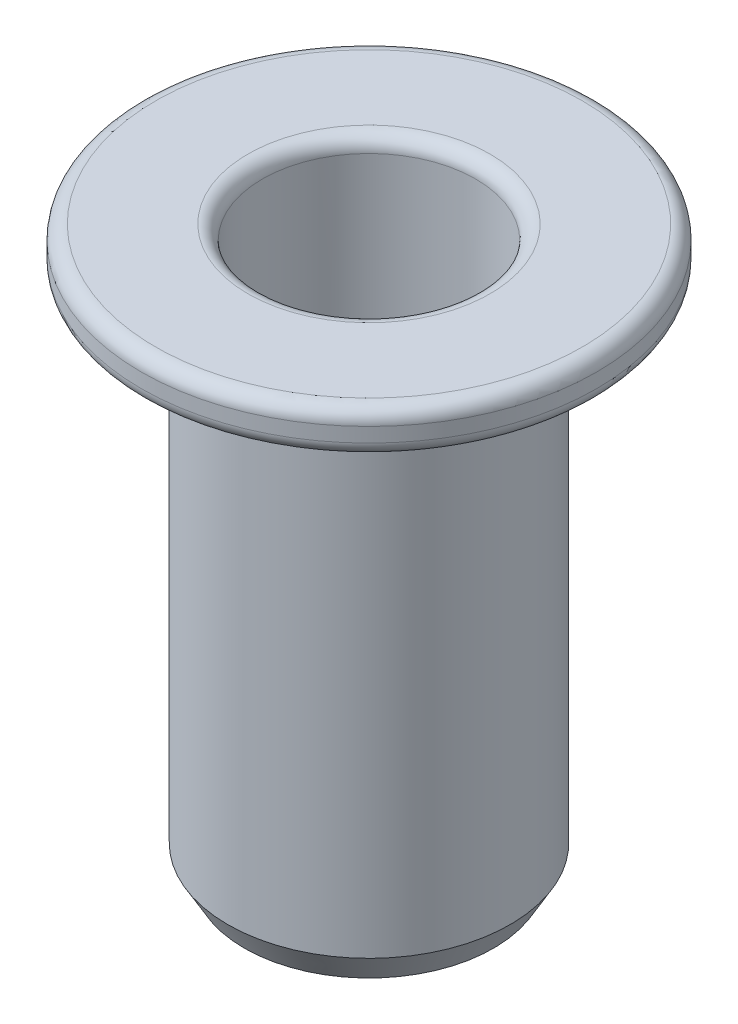
SolidWorks part; units mm, degrees
ref_plane "Front Plane" through (0, 0, 0) normal (0, 0, 1) x (1, 0, 0)
ref_plane "Top Plane" through (0, 0, 0) normal (0, 1, 0) x (1, 0, 0)
ref_plane "Right Plane" through (0, 0, 0) normal (1, 0, 0) x (0, 0, -1)
sketch "Sketch1" plane through (0, 0, 0) normal (0, 0, 1) x (1, 0, 0)
  line L0 (0, 0) -> (0, -9.8) construction
  line L1 (1.85, 0) -> (1.85, -4.5)
  line L2 (1.85, -4.5) -> (1.5, -4.5)
  line L3 (1.5, -4.5) -> (1.5, -9.8)
  line L4 (1.5, -9.8) -> (2.45, -9.8)
  line L5 (2.45, -9.8) -> (2.45, -0.75)
  line L6 (2.45, -0.75) -> (3.95, -0.75)
  line L7 (3.95, -0.75) -> (3.95, 0)
  line L8 (3.95, 0) -> (1.85, 0)
  dimension "D1" = 7.9
  dimension "D2" = 4.9
  dimension "D3" = 0.75
  dimension "D4" = 9.8
  dimension "D5" = 4.5
  dimension "D6" = 3.7
  dimension "D7" = 3
revolve "Revolve1" add sketch "Sketch1" angle 360 about L0
fillet "Fillet1" radius 0.25 3 edges at (0, -0.75, 3.95) (0, 0, 3.95) (0, 0, 1.85)
chamfer "Chamfer1" distance 0.5 angle 30 1 edges at (0, -9.8, 2.45)
chamfer "Chamfer2" distance 0.5 angle 45 1 edges at (0, -9.8, 1.5)
